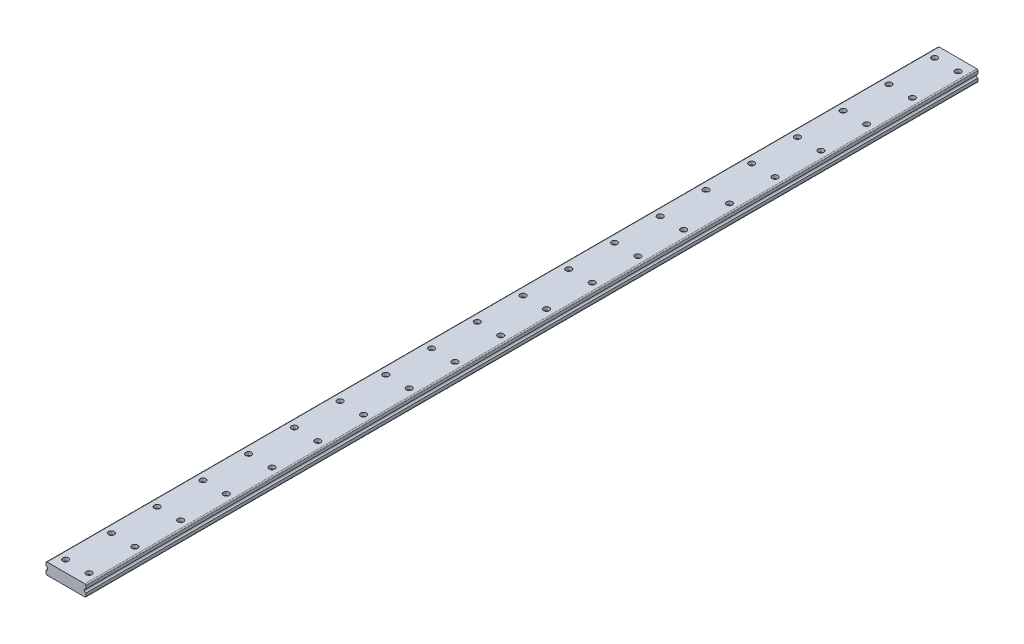
SolidWorks part; units mm, degrees
material "Cast Alloy Steel"
ref_plane "Front Plane" through (0, 0, 0) normal (0, 0, 1) x (1, 0, 0)
ref_plane "Top Plane" through (0, 0, 0) normal (0, 1, 0) x (1, 0, 0)
ref_plane "Right Plane" through (0, 0, 0) normal (1, 0, 0) x (0, 0, -1)
sketch "Sketch1" plane through (0, 0, 0) normal (0, 0, 1) x (1, 0, 0)
  line L0 (0, 13) -> (0, 18)
  line L1 (2, 0) -> (67.85, 0)
  line L2 (0, 2) -> (0, 7)
  line L3 (2, 20) -> (67.85, 20)
  line L4 (69.85, 2) -> (69.85, 7)
  line L5 (69.85, 13) -> (69.85, 18)
  arc A0 (2, 0) -> (0, 2) centre (2, 2) cw
  arc A1 (67.85, 0) -> (69.85, 2) centre (67.85, 2) ccw
  arc A2 (67.85, 20) -> (69.85, 18) centre (67.85, 18) cw
  arc A3 (2, 20) -> (0, 18) centre (2, 18) ccw
  arc A4 (0, 7) -> (0, 13) centre (0, 10) ccw
  arc A5 (69.85, 7) -> (69.85, 13) centre (69.85, 10) cw
  point P7 (0, 0)
  point P10 (69.85, 0)
  point P13 (69.85, 20)
  dimension "D3" = 2
  dimension "D4" = 3
  dimension "D1" = 69.85
  dimension "D2" = 20
  dimension "D5" = 10
extrude "Boss-Extrude1" add sketch "Sketch1" along normal blind 1560.45
sketch "Sketch2" plane through (0, 20, 0) normal (0, 1, 0) x (1, 0, 0)
  line L0 (67.85, -1560.45) -> (2, -1560.45) construction
  circle A0 centre (14.425, -1540.45) radius 5.05
  circle A1 centre (55.425, -1540.45) radius 5.05
  point P7 (34.925, -1560.45)
  dimension "D2" = 10.1
  dimension "D1" = 20
  dimension "D3" = 41
  dimension "D4" = 20.5
extrude "Cut-Extrude1" cut sketch "Sketch2" against normal blind 6
pattern_linear "LPattern1" count 20 spacing 80 along (0, 0, -1) of "Cut-Extrude1"
ref_plane "Plane1" through (34.925, 0, 0) normal (-1, 0, 0) x (0, 0, 1)
